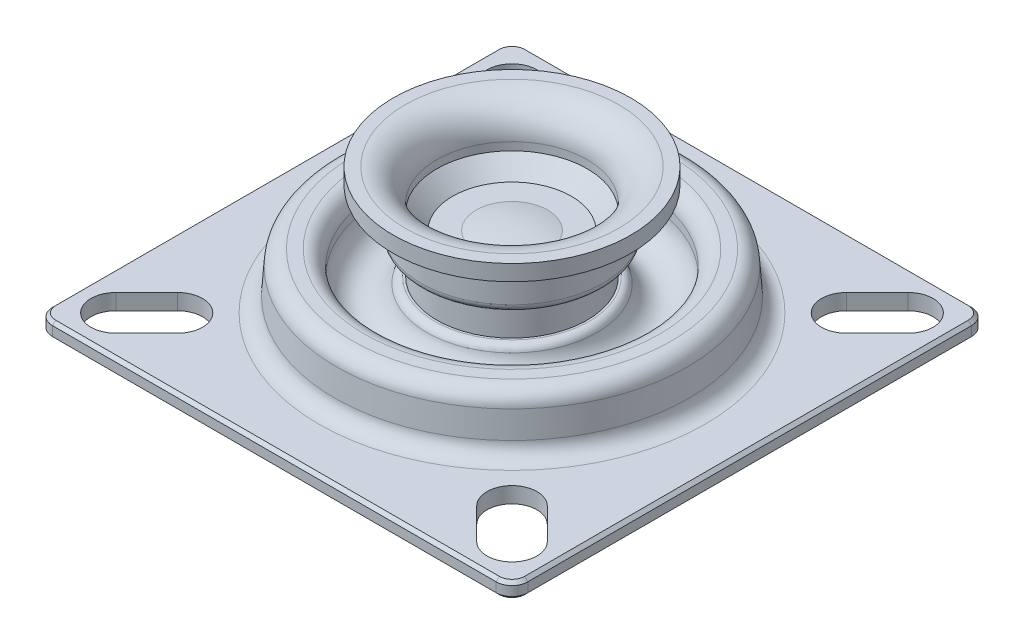
SolidWorks part; units mm, degrees
ref_plane "Plan de face" through (0, 0, 0) normal (0, 0, 1) x (1, 0, 0)
ref_plane "Plan de dessus" through (0, 0, 0) normal (0, 1, 0) x (1, 0, 0)
ref_plane "Plan de droite" through (0, 0, 0) normal (1, 0, 0) x (0, 0, -1)
sketch "Esquisse2" plane through (0, 0, 0) normal (0, 1, 0) x (1, 0, 0)
  line L0 (-25, 25) -> (-21.1109, 21.1109) construction
  line L1 (-30, -30) -> (30, -30)
  line L2 (-30, -30) -> (-30, 30)
  line L3 (-30, 30) -> (30, 30)
  line L4 (30, -30) -> (30, 30)
  line L5 (-30, -30) -> (30, 30) construction
  line L6 (-30, 30) -> (30, -30) construction
  line L7 (-22.7726, 27.2274) -> (-18.8835, 23.3383)
  line L8 (-27.2274, 22.7726) -> (-23.3383, 18.8835)
  line L9 (-27.2274, 27.2274) -> (-18.8835, 18.8835) construction
  line L10 (25, 25) -> (21.1109, 21.1109) construction
  line L11 (27.2274, 22.7726) -> (23.3383, 18.8835)
  line L12 (22.7726, 27.2274) -> (18.8835, 23.3383)
  line L13 (25, -25) -> (21.1109, -21.1109) construction
  line L14 (22.7726, -27.2274) -> (18.8835, -23.3383)
  line L15 (27.2274, -22.7726) -> (23.3383, -18.8835)
  line L16 (-25, -25) -> (-21.1109, -21.1109) construction
  line L17 (-27.2274, -22.7726) -> (-23.3383, -18.8835)
  line L18 (-22.7726, -27.2274) -> (-18.8835, -23.3383)
  arc A0 (-22.7726, 27.2274) -> (-27.2274, 22.7726) centre (-25, 25) ccw
  arc A1 (-23.3383, 18.8835) -> (-18.8835, 23.3383) centre (-21.1109, 21.1109) ccw
  arc A2 (27.2274, 22.7726) -> (22.7726, 27.2274) centre (25, 25) ccw
  arc A3 (18.8835, 23.3383) -> (23.3383, 18.8835) centre (21.1109, 21.1109) ccw
  arc A4 (22.7726, -27.2274) -> (27.2274, -22.7726) centre (25, -25) ccw
  arc A5 (23.3383, -18.8835) -> (18.8835, -23.3383) centre (21.1109, -21.1109) ccw
  arc A6 (-27.2274, -22.7726) -> (-22.7726, -27.2274) centre (-25, -25) ccw
  arc A7 (-18.8835, -23.3383) -> (-23.3383, -18.8835) centre (-21.1109, -21.1109) ccw
  point P0 (0, 0)
  point P8 (-23.0555, 23.0555)
  point P20 (23.0555, 23.0555)
  point P27 (23.0555, -23.0555)
  point P34 (-23.0555, -23.0555)
  point P39 (0, 0)
  dimension "D3" = 3.15
  dimension "D1" = 60
  dimension "D2" = 5
  dimension "D4" = 11.8
  dimension "D5" = 4
extrude "Boss.-Extru.1" add sketch "Esquisse2" along normal mid plane 2
sketch "Esquisse3" plane through (0, 0, 0) normal (0, 0, 1) x (1, 0, 0)
  line L0 (22.5, 1) -> (22.1327, 6.1425)
  line L1 (-30, 1) -> (30, 1) construction
  line L2 (20.1378, 8) -> (0, 8)
  line L4 (0, 8) -> (0, 1)
  line L5 (0, 1) -> (22.5, 1)
  arc A0 (22.1327, 6.1425) -> (20.1378, 8) centre (20.1378, 6) ccw
  point P8 (22, 8)
  dimension "D4" = 2
  dimension "D1" = 22.5
  dimension "D2" = 22
  dimension "D3" = 7
revolve "Révolution1" add sketch "Esquisse3" angle 360 about L4
sketch "Esquisse4" plane through (0, 0, 0) normal (0, 0, 1) x (1, 0, 0)
  line L0 (20.6378, -1) -> (20.1378, 6) construction
  line L1 (-30, -1) -> (30, -1) construction
  line L2 (20.1378, 6) -> (18.1378, 6) construction
  line L3 (18.1378, 6) -> (18.1378, -1) construction
  line L4 (18.1378, -1) -> (8.6378, -1) construction
  line L5 (8.6378, -1) -> (8.6378, 2) construction
  line L6 (8.6378, 2) -> (4.6378, 2)
  line L7 (4.6378, 2) -> (3.5, 3.1378)
  line L8 (3.5, 3.1378) -> (3.5, 6.5)
  line L9 (3.5, 6.5) -> (0, 6.5)
  line L10 (0, 6.5) -> (0, -1) construction
  line L11 (0, 6.5) -> (0, -2)
  line L12 (0, -2) -> (20.6378, -2)
  line L13 (20.6378, -2) -> (20.6378, -1)
  line L14 (22.5, 1) -> (22.1327, 6.1425) construction
  line L15 (20.1378, 8) -> (-20.1378, 8) construction
  line L16 (8.6378, 2) -> (18.1378, 2) construction
  line L17 (18.1378, 2) -> (18.1378, 4.9643)
  line L18 (20.2065, 5.0381) -> (20.6378, -1)
  arc A0 (8.6378, 2) -> (18.1378, 2) centre (13.3878, 4.2604) ccw
  arc A1 (18.1378, 4.9643) -> (20.2065, 5.0381) centre (19.1734, 4.9643) cw
  dimension "D1" = 2
  dimension "D2" = 2
  dimension "D3" = 2
  dimension "D4" = 9.5
  dimension "D5" = 3
  dimension "D6" = 4
  dimension "D7" = 135
  dimension "D8" = 3.5
  dimension "D9" = 4.5
  dimension "D10" = 1
revolve "Enlèvement de matière-Révolution1" cut sketch "Esquisse4" angle 360 about L11
fillet "Congé1" radius 5 1 edges at (-20.6378, -1, 0)
sketch "Esquisse5" plane through (0, 0, 0) normal (0, 0, 1) x (1, 0, 0)
  line L0 (16.6378, 8) -> (16.6378, 4.95)
  line L1 (20.1378, 8) -> (-20.1378, 8) construction
  line L2 (16.6378, 4.95) -> (9.5, 4.95) construction
  line L3 (9.5, 4.95) -> (9.5, 8)
  line L4 (18.1378, 2) -> (18.1378, 4.9643) construction
  line L5 (8.6378, 2) -> (18.1378, 2) construction
  line L6 (3.5, 3.1378) -> (3.5, 6.5) construction
  line L7 (0, 0) -> (0, 8) construction
  line L8 (16.6378, 8) -> (9.5, 8)
  line L9 (9.5, 8) -> (16.6378, 8)
  line L10 (9.7648, 4.95) -> (9.5, 4.95)
  arc A0 (16.6378, 4.95) -> (10.733, 4.2) centre (13.6378, 4.95) cw
  arc A1 (10.733, 4.2) -> (9.7648, 4.95) centre (9.7648, 3.95) ccw
  point P19 (10.6378, 4.95)
  dimension "D4" = 3
  dimension "D5" = 1
  dimension "D1" = 1.5
  dimension "D2" = 2.95
  dimension "D3" = 6
revolve "Enlèvement de matière-Révolution2" cut sketch "Esquisse5" angle 360 about L7
sketch "Esquisse7" plane through (0, 8, 0) normal (0, 1, 0) x (1, 0, 0)
  circle A1 centre (0, 0) radius 9.5
  circle A2 centre (0, 0) radius 9.5
  dimension "D1" = 0
extrude "Boss.-Extru.2" add sketch "Esquisse7" along normal blind 1
fillet "Congé2" radius 2 1 edges at (0, 8, -16.6378)
sketch "Esquisse6" plane through (0, 0, 0) normal (0, 0, 1) x (1, 0, 0)
  line L0 (0, -1) -> (0, 17) construction
  line L1 (-30, -1) -> (30, -1) construction
  line L2 (15, 17) -> (9.5, 17) construction
  line L3 (9.5, 17) -> (9.5, 10) construction
  line L4 (9.5, 10) -> (4.5, 10) construction
  line L5 (4.5, 10) -> (4.5, 10.5) construction
  line L6 (4.5, 10.5) -> (0, 10.5) construction
  line L7 (0, 10.5) -> (0, 9)
  line L8 (0, 9) -> (11.5, 9) construction
  line L10 (13.5, 17) -> (15, 17)
  line L11 (11.5, 9) -> (11.5, 15) construction
  line L12 (11.5, 15) -> (15, 15) construction
  line L13 (15, 15) -> (15, 17)
  line L15 (3.5, 6.5) -> (0, 6.5) construction
  line L16 (13.5, 15) -> (15, 15)
  line L17 (9.5, 13) -> (9.5, 12)
  line L18 (9.5, 12) -> (7.5, 10)
  line L19 (0, 9) -> (10.5, 9)
  line L21 (11.5, 10) -> (11.5, 13)
  line L22 (4.5, 10) -> (7.5, 10)
  line L23 (9.5, 9) -> (-9.5, 9) construction
  arc A0 (9.5, 13) -> (13.5, 17) centre (13.5, 13) cw
  arc A1 (11.5, 13) -> (13.5, 15) centre (13.5, 13) cw
  arc A2 (10.5, 9) -> (11.5, 10) centre (10.5, 10) ccw
  arc A3 (0, 10.5) -> (4.5, 10) centre (0, -10) cw
  dimension "D9" = 4
  dimension "D12" = 1
  dimension "D1" = 18
  dimension "D2" = 4
  dimension "D3" = 4.5
  dimension "D4" = 9.5
  dimension "D5" = 0.5
  dimension "D6" = 30
  dimension "D7" = 2
  dimension "D8" = 2
  dimension "D10" = 45
  dimension "D11" = 2
revolve "Révolution2" add sketch "Esquisse6" angle 360 about L0
fillet "Congé3" radius 2 5 edges at (0, 1, -22.5) (30, 0, 30) (30, 0, -30) (-30, 0, -30) (-30, 0, 30)
chamfer "Chanfrein1" distance 0.4 angle 45 16 edges at (0, -1, -30) (-29.4142, -1, -29.4142) (29.4142, -1, -29.4142) (-30, -1, 0) (30, -1, 0) (-29.4142, -1, 29.4142) (29.4142, -1, 29.4142) (0, -1, 30) (30, 1, 0) (29.4142, 1, -29.4142) (29.4142, 1, 29.4142) (0, 1, -30) (0, 1, 30) (-29.4142, 1, -29.4142) (-29.4142, 1, 29.4142) (-30, 1, 0)
sketch "Esquisse8" plane through (0, 0, 0) normal (0, 0, 1) x (1, 0, 0)
  line L0 (0, 0) -> (0, 4.5) construction
  line L1 (0, 4.5) -> (-13.6, 4.5) construction
  line L3 (0, 4.5) -> (0, 13) construction
  line L4 (0, 13) -> (-13.1, 13) construction
  circle A0 centre (-13.6, 4.5) radius 2.5
  circle A1 centre (-13.1, 13) radius 1.5
  dimension "D1" = 5
  dimension "D4" = 3
  dimension "D2" = 4.5
  dimension "D3" = 13.6
  dimension "D5" = 13.1
  dimension "D6" = 8.5
ref_plane "Plan1" through (0, 4.5, 0) normal (0, 1, 0) x (1, 0, 0)
sketch "Esquisse9" plane through (0, 4.5, 0) normal (0, 1, 0) x (1, 0, 0)
  circle A0 centre (0, 0) radius 13.6 construction
ref_plane "Plan2" through (0, 13, 0) normal (0, 1, 0) x (1, 0, 0)
sketch "Esquisse10" plane through (0, 13, 0) normal (0, 1, 0) x (1, 0, 0)
  circle A0 centre (0, 0) radius 13.1 construction
